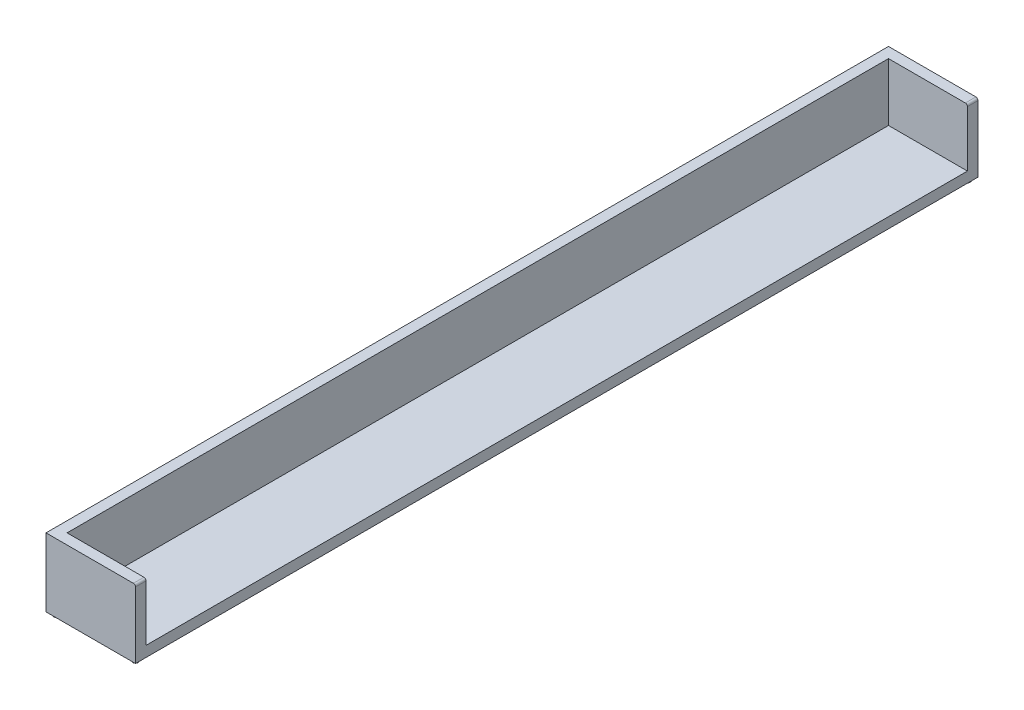
SolidWorks part; units mm, degrees
ref_plane "Front Plane" through (0, 0, 0) normal (0, 0, 1) x (1, 0, 0)
ref_plane "Top Plane" through (0, 0, 0) normal (0, 1, 0) x (1, 0, 0)
ref_plane "Right Plane" through (0, 0, 0) normal (1, 0, 0) x (0, 0, -1)
sketch "Sketch2" plane through (0, 0, 0) normal (0, 0, 1) x (1, 0, 0)
  line L1 (-425, 325) -> (405, 325)
  line L2 (-425, 325) -> (-425, -325)
  line L3 (-425, -325) -> (425, -325)
  line L4 (425, -325) -> (425, 305)
  arc A0 (405, 325) -> (425, 305) centre (405, 305) cw
  point P3 (425, 325)
  point P5 (-10, 325)
  dimension "D3" = 20
  dimension "D1" = 650
  dimension "D2" = 850
extrude "Boss-Extrude1" add sketch "Sketch2" along normal blind 8000
sketch "Sketch3" plane through (0, 325, 0) normal (0, 1, 0) x (1, 0, 0)
  line L0 (-325, -100) -> (-325, -7900)
  line L1 (405, 0) -> (-425, 0) construction
  line L2 (405, -8000) -> (-425, -8000) construction
  line L3 (-425, -8000) -> (-425, 0) construction
  line L4 (-325, -100) -> (425, -100)
  line L5 (425, -100) -> (425, -7900)
  line L6 (425, -7900) -> (-325, -7900)
  dimension "D1" = 100
  dimension "D2" = 100
  dimension "D3" = 100
extrude "Cut-Extrude1" cut sketch "Sketch3" against normal blind 550
sketch "Sketch4" plane through (0, -325, 0) normal (0, -1, 0) x (-1, 0, 0)
  line L0 (425, -8000) -> (-425, -8000) construction
  line L1 (425, -8000) -> (425, 0) construction
  line L2 (-425, -8000) -> (-425, 0) construction
  line L3 (425, 0) -> (-425, 0) construction
  circle A0 centre (375, -7950) radius 25
  circle A1 centre (-375, -7950) radius 25
  circle A2 centre (375, -50) radius 25
  circle A3 centre (-375, -50) radius 25
  circle A4 centre (0, -4000) radius 40
  dimension "D3" = 50
  dimension "D4" = 50
  dimension "D7" = 50
  dimension "D12" = 50
  dimension "D13" = 80
  dimension "D1" = 50
  dimension "D2" = 50
  dimension "D5" = 50
  dimension "D6" = 50
  dimension "D8" = 50
  dimension "D9" = 50
  dimension "D10" = 50
  dimension "D11" = 50
extrude "Boss-Extrude2" add sketch "Sketch4" along normal blind 30
